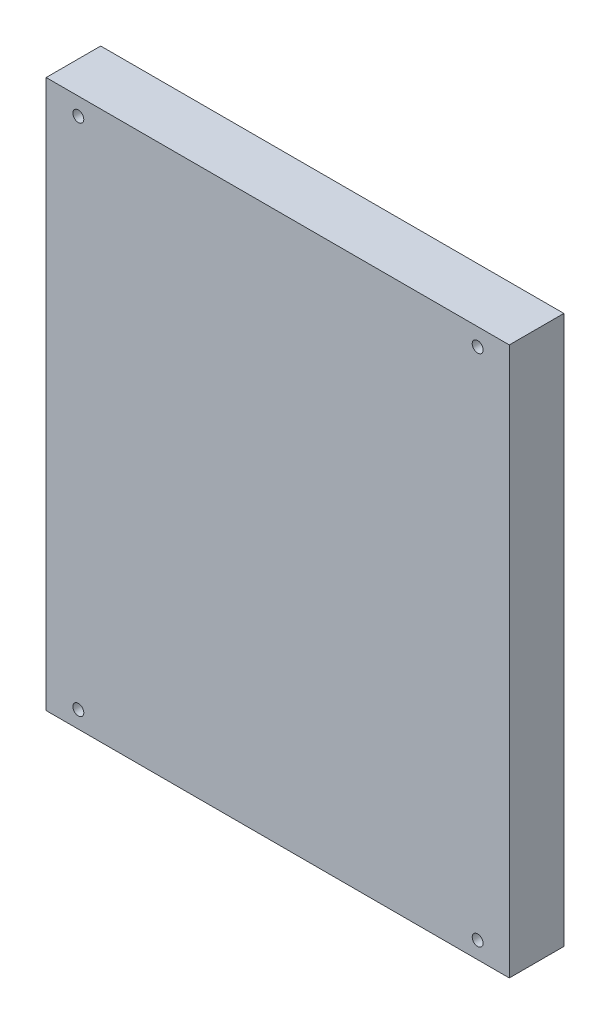
SolidWorks part; units mm, degrees
ref_plane "Plan de face" through (0, 0, 0) normal (0, 0, 1) x (1, 0, 0)
ref_plane "Plan de dessus" through (0, 0, 0) normal (0, 1, 0) x (1, 0, 0)
ref_plane "Plan de droite" through (0, 0, 0) normal (1, 0, 0) x (0, 0, -1)
sketch "Esquisse1" plane through (0, 0, 0) normal (0, 0, 1) x (1, 0, 0)
  line L1 (0, 0) -> (84.9, 0)
  line L2 (0, 0) -> (0, 100.5)
  line L3 (0, 100.5) -> (84.9, 100.5)
  line L4 (84.9, 0) -> (84.9, 100.5)
  dimension "D1" = 100.5
  dimension "D2" = 84.9
extrude "Boss.-Extru.1" add sketch "Esquisse1" along normal blind 10
sketch "Esquisse2" plane through (0, 0, 10) normal (0, 0, 1) x (1, 0, 0)
  line L0 (84.9, 0) -> (84.9, 100.5) construction
  line L1 (84.9, 100.5) -> (0, 100.5) construction
  circle A0 centre (79.1, 97.3) radius 1
  circle A1 centre (5.9, 97.3) radius 1
  circle A2 centre (5.9, 3.1) radius 1
  circle A3 centre (79.1, 3.1) radius 1
  point P6 (0, 0)
  point P7 (0, 0)
  dimension "D1" = 2
  dimension "D2" = 5.8
  dimension "D3" = 3.2
  dimension "D6" = 94.2
  dimension "D7" = 73.2
  dimension "D4" = 2
  dimension "D5" = 2
extrude "Enlèv. mat.-Extru.1" cut sketch "Esquisse2" against normal through all
